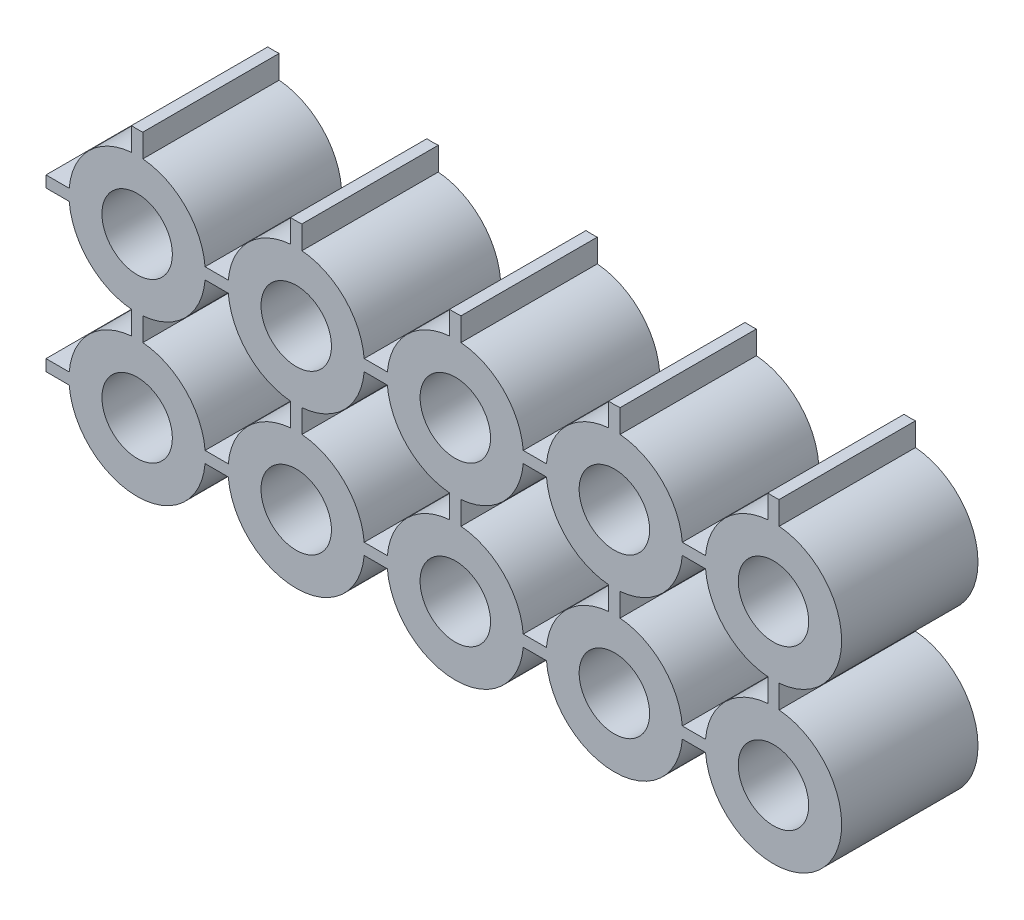
SolidWorks part; units mm, degrees
ref_plane "Plan de face" through (0, 0, 0) normal (0, 0, 1) x (1, 0, 0)
ref_plane "Plan de dessus" through (0, 0, 0) normal (0, 1, 0) x (1, 0, 0)
ref_plane "Plan de droite" through (0, 0, 0) normal (1, 0, 0) x (0, 0, -1)
sketch "Esquisse1" plane through (0, 0, 0) normal (0, 0, 1) x (1, 0, 0)
  line L0 (-0.25, 4.0104) -> (-0.25, 2.9896)
  line L1 (0.25, 4.0104) -> (0.25, 2.9896)
  line L2 (0, 0) -> (0, 5.9789) construction
  line L3 (-4.0104, -0.25) -> (-2.9896, -0.25)
  line L4 (-4.0104, 0.25) -> (-2.9896, 0.25)
  arc A0 (-0.25, 2.9896) -> (-2.9896, 0.25) centre (0, 0) ccw
  circle A1 centre (0, 0) radius 1.55
  circle A2 centre (0, 7) radius 3 construction
  arc A3 (-0.25, 4.0104) -> (0.25, 4.0104) centre (0, 7) ccw
  arc A4 (-4.0104, -0.25) -> (-4.0104, 0.25) centre (-7, 0) ccw
  arc A5 (-2.9896, -0.25) -> (0.25, 2.9896) centre (0, 0) ccw
  point P17 (0, 0)
  dimension "D1" = 3.1
  dimension "D2" = 6
  dimension "D4" = 6
  dimension "D7" = 2
  dimension "D3" = 7
  dimension "D5" = 0.5
  dimension "D6" = 0.25
extrude "Boss.-Extru.2" add sketch "Esquisse1" along normal blind 6
pattern_linear "Répétition linéaire1" count 2 spacing 7 along (0, -1, 0) count 5 spacing 7 along (1, 0, 0) of "Boss.-Extru.2"
equation "\"D6@Esquisse1\"=\"D5@Esquisse1\"/2"
